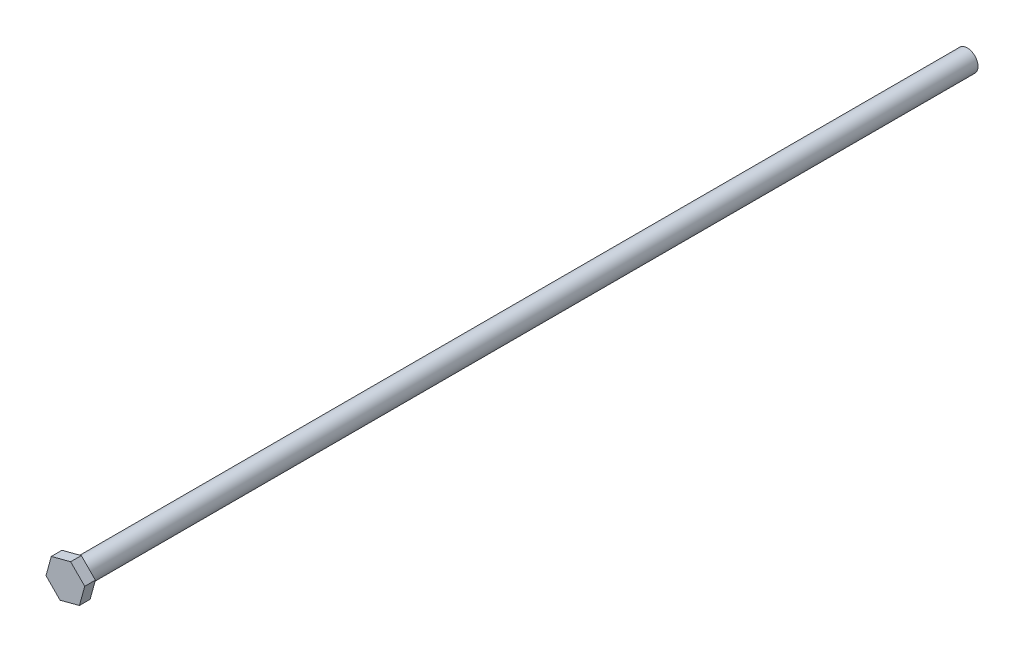
SolidWorks part; units mm, degrees
ref_plane "Front Plane" through (0, 0, 0) normal (0, 0, 1) x (1, 0, 0)
ref_plane "Top Plane" through (0, 0, 0) normal (0, 1, 0) x (1, 0, 0)
ref_plane "Right Plane" through (0, 0, 0) normal (1, 0, 0) x (0, 0, -1)
sketch "Sketch1" plane through (0, 0, 0) normal (0, 0, 1) x (1, 0, 0)
  circle A0 centre (0, 0) radius 2
  dimension "D1" = 4
extrude "Boss-Extrude1" add sketch "Sketch1" along normal blind 167
sketch "Sketch2" plane through (0, 0, 167) normal (0, 0, 1) x (1, 0, 0)
  line L0 (0, 0) -> (-2.6358, 2.6674) construction
  line L1 (0, 0) -> (0.9921, 3.6164) construction
  line L2 (0, 0) -> (3.6279, 0.949) construction
  line L3 (0, 0) -> (2.6358, -2.6674) construction
  line L4 (0, 0) -> (-0.9921, -3.6164) construction
  line L5 (-2.6358, 2.6674) -> (0.9921, 3.6164)
  line L6 (0.9921, 3.6164) -> (3.6279, 0.949)
  line L7 (3.6279, 0.949) -> (2.6358, -2.6674)
  line L8 (2.6358, -2.6674) -> (-0.9921, -3.6164)
  line L9 (0, 0) -> (-3.6279, -0.949) construction
  line L10 (-0.9921, -3.6164) -> (-3.6279, -0.949)
  line L11 (-3.6279, -0.949) -> (-2.6358, 2.6674)
  point P9 (0, 0)
  dimension "D1" = 3.75
  dimension "D2" = 6
extrude "Boss-Extrude2" add sketch "Sketch2" along normal blind 2
